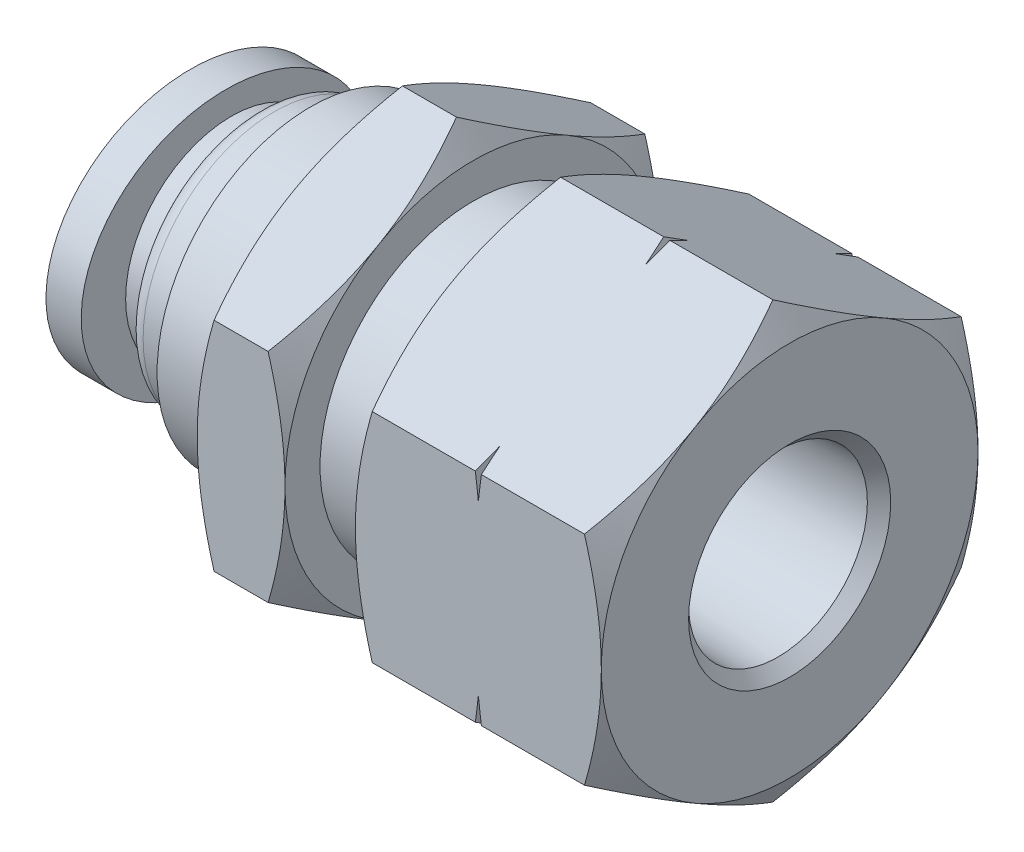
SolidWorks part; units mm, degrees
material "6061-T6 (SS)"
ref_plane "Front Plane" through (0, 0, 0) normal (0, 0, 1) x (1, 0, 0)
ref_plane "Top Plane" through (0, 0, 0) normal (0, 1, 0) x (1, 0, 0)
ref_plane "Right Plane" through (0, 0, 0) normal (1, 0, 0) x (0, 0, -1)
sketch "Sketch1" plane through (0, 0, 0) normal (1, 0, 0) x (0, 0, -1)
  line L1 (0, 9.796) -> (-8.4836, 4.898)
  line L2 (-8.4836, 4.898) -> (-8.4836, -4.898)
  line L3 (-8.4836, -4.898) -> (0, -9.796)
  line L4 (0, -9.796) -> (8.4836, -4.898)
  line L5 (8.4836, -4.898) -> (8.4836, 4.898)
  line L6 (8.4836, 4.898) -> (0, 9.796)
  circle A0 centre (0, 0) radius 8.4836 construction
  dimension "D1" = 16.9672
extrude "Boss-Extrude1" add sketch "Sketch1" along normal mid plane 26.9875
sketch "Sketch2" plane through (0, 0, 0) normal (0, 0, 1) x (1, 0, 0)
  line L0 (13.4937, 0) -> (-13.4937, 0) construction
  line L1 (13.4937, 4.898) -> (13.4937, -4.898) construction
  line L2 (-13.4937, 4.898) -> (-13.4937, -4.898) construction
  line L3 (13.4937, 9.796) -> (13.4937, 8.4836)
  line L4 (13.4937, 9.796) -> (13.4937, 4.898) construction
  line L5 (13.4937, 8.4836) -> (12.736, 9.796)
  line L6 (13.4937, 9.796) -> (-13.4937, 9.796) construction
  line L7 (12.736, 9.796) -> (13.4937, 9.796)
  line L8 (3.1771, 9.796) -> (-1.5134, 9.796)
  line L9 (-1.5134, 9.796) -> (-0.7557, 8.4836)
  line L10 (-0.7557, 8.4836) -> (-0.7557, 6.9024)
  line L11 (-0.7557, 6.9024) -> (2.4193, 6.9024)
  line L12 (2.4193, 6.9024) -> (2.4193, 8.4836)
  line L13 (2.4193, 8.4836) -> (3.1771, 9.796)
  line L14 (7.8204, 9.796) -> (7.9566, 9.288)
  line L15 (7.9566, 9.288) -> (8.0927, 9.796)
  line L16 (8.0927, 9.796) -> (7.8204, 9.796)
  line L17 (-3.9476, 9.796) -> (-4.7053, 8.4836)
  line L18 (-4.7053, 8.4836) -> (-4.7053, 6.9024)
  line L19 (-4.7053, 6.9024) -> (-8.0962, 6.9024)
  line L20 (-8.0962, 6.9024) -> (-8.0962, 5.9055)
  line L21 (-8.0962, 5.9055) -> (-9.7218, 5.9055)
  line L22 (-10.4838, 5.1435) -> (-10.4838, 4.7625)
  line L23 (-10.4838, 4.7625) -> (-11.6522, 4.7625)
  line L24 (-11.6522, 4.7625) -> (-11.6522, 3.81)
  line L25 (-11.6522, 3.81) -> (-13.4937, 3.81)
  line L26 (2.8838, 9.288) -> (13.0293, 9.288) construction
  line L27 (13.4937, 4.0437) -> (4.1973, 3.7401)
  line L28 (4.1973, 3.7401) -> (3.4971, 2.5273)
  line L29 (3.4971, 2.5273) -> (2.2542, 2.5273)
  line L30 (2.2542, 2.5273) -> (2.2542, 3.81)
  line L31 (-13.4937, 0) -> (-13.4937, 3.3147)
  line L32 (-13.4937, 3.3147) -> (-5.8737, 3.3147)
  line L33 (-5.8737, 3.3147) -> (-5.8737, 3.81)
  line L34 (-5.8737, 3.81) -> (2.2542, 3.81)
  line L35 (13.4937, 4.0437) -> (13.4937, 0)
  line L36 (13.4937, 0) -> (-13.4937, 0)
  line L37 (-13.4937, 3.81) -> (-13.4937, 9.796)
  line L38 (-13.4937, 9.796) -> (-3.9476, 9.796)
  arc A0 (-9.7218, 5.9055) -> (-10.4838, 5.1435) centre (-9.7218, 5.1435) ccw
  dimension "D13" = 0.762
  dimension "D1" = 30
  dimension "D2" = 0.508
  dimension "D3" = 60
  dimension "D4" = 11.0744
  dimension "D5" = 16.9672
  dimension "D6" = 13.8049
  dimension "D7" = 3.175
  dimension "D8" = 3.9497
  dimension "D9" = 11.811
  dimension "D10" = 23.9776
  dimension "D11" = 21.59
  dimension "D12" = 9.525
  dimension "D14" = 7.62
  dimension "D15" = 25.146
  dimension "D16" = 1.87
  dimension "D17" = 7.4803
  dimension "D18" = 9.2964
  dimension "D19" = 60
  dimension "D20" = 5.0546
  dimension "D21" = 6.6294
  dimension "D22" = 15.748
  dimension "D23" = 7.62
revolve "Cut-Revolve1" cut sketch "Sketch2" angle 360 about L36
chamfer "Chamfer1" distance 0.508 angle 45 1 edges at (13.4937, 0, -4.0437)
sketch "Sketch3" plane through (-13.4937, 0, 0) normal (-1, 0, 0) x (0, 0, 1)
  circle A0 centre (0, 0) radius 3.3147 construction
  circle A1 centre (0, 0) radius 3.3147
  ellipse E0 centre (0, 0) end of major axis (-6.5088, 0) minor radius 5.6769
  point P1 (6.4131, 1.1116)
  dimension "D1" = 13.0175
  dimension "D2" = 11.3538
extrude "Boss-Extrude2" add sketch "Sketch3" against normal blind 1.5875
